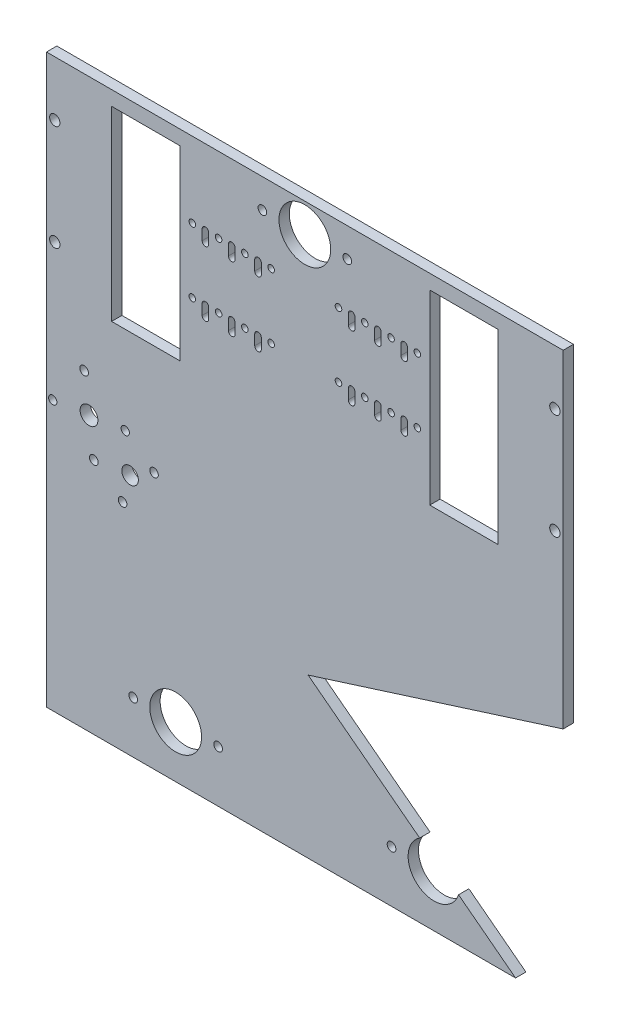
SolidWorks part; units mm, degrees
ref_plane "Front Plane" through (0, 0, 0) normal (0, 0, 1) x (1, 0, 0)
ref_plane "Top Plane" through (0, 0, 0) normal (0, 1, 0) x (1, 0, 0)
ref_plane "Right Plane" through (0, 0, 0) normal (1, 0, 0) x (0, 0, -1)
sketch "Sketch1" plane through (0, 0, 0) normal (0, 0, 1) x (1, 0, 0)
  line L0 (124.8, 0) -> (124.8, -340.9) construction
  line L1 (0, 0) -> (249.6, 0)
  line L2 (0, 0) -> (0, -340.9)
  line L3 (0, -340.9) -> (249.6, -340.9)
  line L4 (249.6, 0) -> (249.6, -340.9)
  line L9 (185.16, -7) -> (218.16, -7)
  line L10 (185.16, -7) -> (185.16, -97)
  line L11 (185.16, -97) -> (218.16, -97)
  line L12 (218.16, -7) -> (218.16, -97)
  line L13 (179.16, -52) -> (228.95, -52) construction
  line L14 (141.06, -36.375) -> (147.41, -36.375) construction
  line L15 (145.3, -14) -> (104.3, -14) construction
  line L21 (179.16, -52) -> (218.16, -52) construction
  line L25 (141.06, -67.625) -> (147.41, -67.625) construction
  line L32 (147.41, -36.375) -> (147.41, -41.375) construction
  line L33 (145.8225, -36.375) -> (145.8225, -41.375)
  line L34 (148.9975, -36.375) -> (148.9975, -41.375)
  line L35 (160.11, -36.375) -> (160.11, -41.375) construction
  line L36 (158.52, -36.375) -> (158.52, -41.375)
  line L37 (161.7, -36.375) -> (161.7, -41.375)
  line L38 (172.81, -36.375) -> (172.81, -41.375) construction
  line L39 (171.22, -36.375) -> (171.22, -41.375)
  line L40 (174.4, -36.375) -> (174.4, -41.375)
  line L41 (147.41, -36.375) -> (153.76, -36.375) construction
  line L42 (153.76, -36.375) -> (160.11, -36.375) construction
  line L43 (160.11, -36.375) -> (166.46, -36.375) construction
  line L44 (166.46, -36.375) -> (172.81, -36.375) construction
  line L45 (172.81, -36.375) -> (179.16, -36.375) construction
  line L48 (228.95, -52) -> (147.41, -52) construction
  line L52 (204.16, -7) -> (204.16, -97) construction
  line L53 (194.16, -7) -> (214.16, -7) construction
  line L54 (194.16, -7) -> (194.16, -97) construction
  line L55 (194.16, -97) -> (214.16, -97) construction
  line L56 (214.16, -7) -> (214.16, -97) construction
  line L62 (147.41, -67.625) -> (147.41, -72.625) construction
  line L65 (145.8225, -67.625) -> (145.8225, -72.625)
  line L68 (148.9975, -67.625) -> (148.9975, -72.625)
  line L71 (160.11, -67.625) -> (160.11, -72.625) construction
  line L78 (158.52, -67.625) -> (158.52, -72.625)
  line L79 (161.7, -67.625) -> (161.7, -72.625)
  line L80 (172.81, -67.625) -> (172.81, -72.625) construction
  line L83 (171.22, -67.625) -> (171.22, -72.625)
  line L87 (147.41, -52) -> (102.19, -52) construction
  line L90 (179.16, -36.375) -> (179.16, -67.625) construction
  line L93 (147.41, -36.375) -> (147.41, -52) construction
  line L102 (245.6, -26.5) -> (245.6, -77.5) construction
  line L103 (218.16, -52) -> (245.6, -52) construction
  line L105 (174.4, -67.625) -> (174.4, -72.625)
  line L106 (147.41, -67.625) -> (153.76, -67.625) construction
  line L107 (153.76, -67.625) -> (160.11, -67.625) construction
  line L108 (160.11, -67.625) -> (166.46, -67.625) construction
  line L109 (166.46, -67.625) -> (172.81, -67.625) construction
  line L110 (172.81, -67.625) -> (179.16, -67.625) construction
  line L111 (102.19, -36.375) -> (102.19, -41.375) construction
  line L112 (103.7775, -36.375) -> (103.7775, -41.375)
  line L113 (100.6025, -36.375) -> (100.6025, -41.375)
  line L114 (89.49, -36.375) -> (89.49, -41.375) construction
  line L115 (91.08, -36.375) -> (91.08, -41.375)
  line L116 (87.9, -36.375) -> (87.9, -41.375)
  line L117 (76.79, -36.375) -> (76.79, -41.375) construction
  line L118 (78.38, -36.375) -> (78.38, -41.375)
  line L119 (75.2, -36.375) -> (75.2, -41.375)
  line L120 (102.19, -67.625) -> (102.19, -72.625) construction
  line L121 (103.7775, -67.625) -> (103.7775, -72.625)
  line L122 (100.6025, -67.625) -> (100.6025, -72.625)
  line L123 (89.49, -67.625) -> (89.49, -72.625) construction
  line L124 (91.08, -67.625) -> (91.08, -72.625)
  line L125 (87.9, -67.625) -> (87.9, -72.625)
  line L126 (76.79, -67.625) -> (76.79, -72.625) construction
  line L127 (78.38, -67.625) -> (78.38, -72.625)
  line L128 (75.2, -67.625) -> (75.2, -72.625)
  line L129 (76.79, -67.625) -> (70.44, -67.625) construction
  line L130 (83.14, -67.625) -> (76.79, -67.625) construction
  line L131 (89.49, -67.625) -> (83.14, -67.625) construction
  line L132 (95.84, -67.625) -> (89.49, -67.625) construction
  line L133 (102.19, -67.625) -> (95.84, -67.625) construction
  line L134 (31.44, -52) -> (4, -52) construction
  line L135 (4, -26.5) -> (4, -77.5) construction
  line L136 (102.19, -36.375) -> (102.19, -52) construction
  line L137 (70.44, -36.375) -> (70.44, -67.625) construction
  line L139 (35.44, -7) -> (35.44, -97) construction
  line L140 (55.44, -97) -> (35.44, -97) construction
  line L141 (55.44, -7) -> (55.44, -97) construction
  line L142 (55.44, -7) -> (35.44, -7) construction
  line L143 (45.44, -7) -> (45.44, -97) construction
  line L144 (20.65, -52) -> (102.19, -52) construction
  line L145 (76.79, -36.375) -> (70.44, -36.375) construction
  line L146 (83.14, -36.375) -> (76.79, -36.375) construction
  line L147 (89.49, -36.375) -> (83.14, -36.375) construction
  line L148 (95.84, -36.375) -> (89.49, -36.375) construction
  line L149 (102.19, -36.375) -> (95.84, -36.375) construction
  line L150 (108.54, -67.625) -> (102.19, -67.625) construction
  line L151 (70.44, -52) -> (31.44, -52) construction
  line L152 (108.54, -36.375) -> (102.19, -36.375) construction
  line L153 (70.44, -52) -> (20.65, -52) construction
  line L154 (31.44, -7) -> (31.44, -97)
  line L155 (64.44, -97) -> (31.44, -97)
  line L156 (64.44, -7) -> (64.44, -97)
  line L157 (64.44, -7) -> (31.44, -7)
  arc A6 (174.4, -36.375) -> (171.22, -36.375) centre (172.81, -36.375) cw construction
  arc A7 (171.22, -36.375) -> (174.4, -36.375) centre (172.81, -36.375) cw
  arc A10 (158.52, -36.375) -> (161.7, -36.375) centre (160.11, -36.375) cw
  arc A11 (161.7, -36.375) -> (158.52, -36.375) centre (160.11, -36.375) cw construction
  arc A14 (145.8225, -36.375) -> (148.9975, -36.375) centre (147.41, -36.375) cw
  arc A15 (148.9975, -36.375) -> (145.8225, -36.375) centre (147.41, -36.375) cw construction
  circle A38 centre (104.3, -14) radius 2.1
  arc A39 (148.9975, -41.375) -> (145.8225, -41.375) centre (147.41, -41.375) cw
  arc A41 (161.7, -41.375) -> (158.52, -41.375) centre (160.11, -41.375) cw
  arc A43 (174.4, -41.375) -> (171.22, -41.375) centre (172.81, -41.375) cw
  circle A84 centre (245.6, -26.5) radius 2.5
  circle A85 centre (245.6, -77.5) radius 2.5
  circle A109 centre (145.3, -14) radius 2.1
  circle A179 centre (179.16, -36.375) radius 1.59
  arc A182 (174.4, -67.625) -> (171.22, -67.625) centre (172.81, -67.625) cw construction
  arc A183 (171.22, -67.625) -> (174.4, -67.625) centre (172.81, -67.625) cw
  arc A184 (158.52, -67.625) -> (161.7, -67.625) centre (160.11, -67.625) cw
  arc A185 (161.7, -67.625) -> (158.52, -67.625) centre (160.11, -67.625) cw construction
  arc A188 (145.8225, -67.625) -> (148.9975, -67.625) centre (147.41, -67.625) cw
  arc A189 (148.9975, -67.625) -> (145.8225, -67.625) centre (147.41, -67.625) cw construction
  arc A193 (148.9975, -72.625) -> (145.8225, -72.625) centre (147.41, -72.625) cw
  arc A195 (161.7, -72.625) -> (158.52, -72.625) centre (160.11, -72.625) cw
  arc A197 (174.4, -72.625) -> (171.22, -72.625) centre (172.81, -72.625) cw
  circle A198 centre (179.16, -67.625) radius 1.59
  circle A199 centre (124.8, -14) radius 12.5
  circle A200 centre (141.06, -36.375) radius 1.59
  circle A201 centre (153.76, -36.375) radius 1.59
  circle A202 centre (166.46, -36.375) radius 1.59
  circle A203 centre (141.06, -67.625) radius 1.59
  circle A204 centre (153.76, -67.625) radius 1.59
  circle A205 centre (166.46, -67.625) radius 1.59
  arc A206 (103.7775, -36.375) -> (100.6025, -36.375) centre (102.19, -36.375) ccw
  arc A207 (100.6025, -41.375) -> (103.7775, -41.375) centre (102.19, -41.375) ccw
  arc A208 (91.08, -36.375) -> (87.9, -36.375) centre (89.49, -36.375) ccw
  arc A209 (87.9, -41.375) -> (91.08, -41.375) centre (89.49, -41.375) ccw
  arc A210 (78.38, -36.375) -> (75.2, -36.375) centre (76.79, -36.375) ccw
  arc A211 (75.2, -41.375) -> (78.38, -41.375) centre (76.79, -41.375) ccw
  arc A212 (103.7775, -67.625) -> (100.6025, -67.625) centre (102.19, -67.625) ccw
  arc A213 (100.6025, -72.625) -> (103.7775, -72.625) centre (102.19, -72.625) ccw
  arc A214 (91.08, -67.625) -> (87.9, -67.625) centre (89.49, -67.625) ccw
  arc A215 (87.9, -72.625) -> (91.08, -72.625) centre (89.49, -72.625) ccw
  arc A216 (78.38, -67.625) -> (75.2, -67.625) centre (76.79, -67.625) ccw
  arc A217 (75.2, -72.625) -> (78.38, -72.625) centre (76.79, -72.625) ccw
  arc A218 (100.6025, -67.625) -> (103.7775, -67.625) centre (102.19, -67.625) ccw construction
  arc A219 (87.9, -67.625) -> (91.08, -67.625) centre (89.49, -67.625) ccw construction
  arc A220 (75.2, -67.625) -> (78.38, -67.625) centre (76.79, -67.625) ccw construction
  arc A221 (100.6025, -36.375) -> (103.7775, -36.375) centre (102.19, -36.375) ccw construction
  arc A222 (87.9, -36.375) -> (91.08, -36.375) centre (89.49, -36.375) ccw construction
  arc A223 (75.2, -36.375) -> (78.38, -36.375) centre (76.79, -36.375) ccw construction
  circle A224 centre (83.14, -67.625) radius 1.59
  circle A225 centre (95.84, -67.625) radius 1.59
  circle A226 centre (108.54, -67.625) radius 1.59
  circle A227 centre (83.14, -36.375) radius 1.59
  circle A228 centre (95.84, -36.375) radius 1.59
  circle A229 centre (108.54, -36.375) radius 1.59
  circle A230 centre (70.44, -67.625) radius 1.59
  circle A234 centre (70.44, -36.375) radius 1.59
  circle A236 centre (4, -77.5) radius 2.5
  circle A237 centre (4, -26.5) radius 2.5
  point P64 (147.41, -52)
  point P65 (102.19, -38.875)
  point P69 (228.95, -52)
  point P71 (221, -87.34)
  point P76 (233.7, -87.34)
  point P78 (221, -54.5)
  point P82 (233.7, -54.5)
  point P86 (246.4, -54.5)
  point P93 (179.16, -52)
  point P97 (246.4, -87.34)
  point P104 (89.49, -38.875)
  point P111 (76.79, -38.875)
  point P119 (102.19, -70.125)
  point P126 (89.49, -70.125)
  point P133 (76.79, -70.125)
  point P155 (124.8, -76.5574)
  point P166 (124.8, -52)
  point P183 (124.8, -76.5574)
  point P199 (70.44, -52)
  point P200 (20.65, -52)
  point P201 (102.19, -52)
  dimension "D5" = 20
  dimension "D10" = 5
  dimension "D12" = 3.18
  dimension "D15" = 5
  dimension "D16" = 5
  dimension "D19" = 3.18
  dimension "D20" = 1.5875
  dimension "D21" = 3.18
  dimension "D22" = 1.59
  dimension "D23" = 3.18
  dimension "D24" = 1.59
  dimension "D25" = 3.18
  dimension "D33" = 3.18
  dimension "D34" = 5
  dimension "D35" = 4.2
  dimension "D32" = 1.5875
  dimension "D36" = 1.59
  dimension "D37" = 3.18
  dimension "D39" = 1.59
  dimension "D47" = 3.18
  dimension "D49" = 25
  dimension "D51" = 4.2
  dimension "D1" = 249.6
  dimension "D2" = 340.9
  dimension "D3" = 4
  dimension "D4" = 90
  dimension "D6" = 90
  dimension "D7" = 9
  dimension "D8" = 6
  dimension "D9" = 5
  dimension "D11" = 6.35
  dimension "D13" = 6.35
  dimension "D14" = 89.36
  dimension "D17" = 25.5
  dimension "D18" = 4
  dimension "D26" = 5
  dimension "D27" = 6.35
  dimension "D28" = 6.35
  dimension "D29" = 6.35
  dimension "D30" = 6.35
  dimension "D31" = 6.35
  dimension "D38" = 7
  dimension "D40" = 5
  dimension "D41" = 6.35
  dimension "D42" = 6.35
  dimension "D43" = 6.35
  dimension "D44" = 6.35
  dimension "D45" = 6.35
  dimension "D46" = 5
  dimension "D48" = 31.25
  dimension "D50" = 20.5
  dimension "14" = 14
extrude "Boss-Extrude1" add sketch "Sketch1" along normal blind 5
sketch "Sketch2" plane through (0, 0, 5) normal (0, 0, 1) x (1, 0, 0)
  line L0 (-27.1214, -80.1211) -> (54.8789, 27.1214) construction
  line L1 (277.1296, -312.7589) -> (359.1299, -205.5164) construction
  line L2 (-27.1214, -80.1211) -> (277.1296, -312.7589) construction
  line L3 (92.2198, 60.8405) -> (87.5714, 58.9986) construction
  line L4 (87.5714, 58.9986) -> (112.9306, -5) construction
  line L5 (120.7692, -11.2093) -> (92.2198, 60.8405) construction
  line L6 (54.8789, 27.1214) -> (359.1299, -205.5164) construction
  line L7 (51.8418, 23.1494) -> (356.0928, -209.4884) construction
  line L8 (-24.0843, -76.1492) -> (280.1666, -308.787) construction
  line L9 (92.2198, 60.8405) -> (96.8682, 62.6824) construction
  line L10 (96.8682, 62.6824) -> (122.2273, -1.3162) construction
  line L11 (178.4848, -231.0386) -> (254.411, -131.74) construction
  line L12 (117.1493, -105.4631) -> (216.4479, -181.3893) construction
  line L13 (79.1862, -155.1124) -> (155.1124, -55.8138) construction
  line L14 (249.6, 0) -> (0, 0) construction
  line L15 (0, 0) -> (0, -340.9) construction
  line L16 (5, -130) -> (130, -130) construction
  line L17 (5, -340.9) -> (5, 0) construction
  line L18 (130, -340.9) -> (130, 0) construction
  line L19 (0, -340.9) -> (0, 0) construction
  line L20 (135, -340.9) -> (135, 0) construction
  line L21 (0, -340.9) -> (33.4202, -340.9) construction
  line L22 (33.4202, -340.9) -> (130, -340.9) construction
  line L23 (130, -340.9) -> (135, -340.9) construction
  line L24 (0, -340.9) -> (249.6, -340.9) construction
  line L25 (0, 0) -> (5, 0) construction
  line L26 (5, 0) -> (130, 0) construction
  line L27 (130, 0) -> (135, 0) construction
  line L28 (249.6, -98.5967) -> (312.6149, -98.5967) construction
  line L29 (249.6, -340.9) -> (249.6, 0) construction
  line L30 (249.6, -158.6746) -> (295.6765, -158.6746) construction
  line L31 (185.16, -97) -> (218.16, -97) construction
  line L32 (194.16, -7.496) -> (194.16, -96.496) construction
  line L33 (180.868, -232.8608) -> (256.7942, -133.5622) construction
  line L34 (249.6, -283.6746) -> (0, -283.6746) construction
  line L35 (0, -5) -> (249.6, -5) construction
  line L36 (249.6, 0) -> (249.6, -5) construction
  line L37 (249.6, -5) -> (249.6, -340.9) construction
  line L38 (249.6, -340.9) -> (5, -340.9) construction
  line L39 (5, -340.9) -> (0, -340.9) construction
  line L40 (0, -335.9) -> (249.6, -335.9) construction
  line L41 (244.6, -340.9) -> (244.6, 0) construction
  circle A0 centre (67.5, -67.5) radius 62.5 construction
  circle A1 centre (268.4804, -221.1746) radius 62.5 construction
  circle A2 centre (67.5, -67.5) radius 67.5 construction
  circle A3 centre (166.7986, -143.4262) radius 62.5 construction
  circle A4 centre (120.7692, -11.2093) radius 77.5 construction
  circle A5 centre (120.7692, -11.2093) radius 2.5 construction
  circle A6 centre (111.5597, 12.0326) radius 1.5 construction
  arc A7 (112.9306, -5) -> (122.2273, -1.3162) centre (120.7692, -11.2093) ccw construction
  point P49 (194.16, -97)
  dimension "D1" = 125
  dimension "D2" = 125
  dimension "D3" = 5
  dimension "D6" = 3
  dimension "D7" = 10
  dimension "D10" = 125
  dimension "D8" = 5
  dimension "D11" = 3
  dimension "D4" = 5
  dimension "D5" = 25
  dimension "D9" = 5
  dimension "D12" = 14
  dimension "D13" = 5
  dimension "D14" = 5
  dimension "D15" = 5
  dimension "D16" = 5
  dimension "D17" = 5
sketch "Sketch4" plane through (0, 0, 5) normal (0, 0, 1) x (1, 0, 0)
  line L3 (249.6, -161.5945) -> (249.6, -280.7546)
  line L5 (249.6, -340.9) -> (249.6, 0) construction
  arc A0 (249.6, -161.5945) -> (249.6, -280.7546) centre (268.4804, -221.1746) ccw
  circle A1 centre (268.4804, -221.1746) radius 62.5 construction
extrude "Cut-Extrude3" cut sketch "Sketch4" along normal blind 193 and the other way blind 193
sketch "Sketch7" plane through (0, 0, 5) normal (0, 0, 1) x (1, 0, 0)
  line L0 (249.6, -158.4475) -> (126.3826, -197.4941)
  line L1 (249.6, -340.9) -> (249.6, -280.7546) construction
  line L2 (126.3826, -197.4941) -> (249.6, -158.4475) construction
  line L3 (-27.1214, -80.1211) -> (277.1296, -312.7589) construction
  line L4 (126.3826, -197.4941) -> (226.6086, -274.1293)
  line L5 (249.6, -158.4475) -> (249.6, -340.9)
  line L6 (249.6, -340.9) -> (0, -340.9)
  line L7 (0, -340.9) -> (0, -274.1293)
  line L10 (0, -340.9) -> (249.6, -340.9) construction
  line L11 (0, 0) -> (0, -340.9) construction
  line L12 (226.6086, -274.1293) -> (0, -274.1293)
extrude "Cut-Extrude6" cut sketch "Sketch7" against normal through all
sketch "Sketch8" plane through (0, 0, 5) normal (0, 0, 1) x (1, 0, 0)
  circle A0 centre (3.009, -144.0715) radius 2
  circle A1 centre (18.1942, -124.2118) radius 2.1
  circle A2 centre (22.8687, -159.2567) radius 2.1
  circle A3 centre (36.7705, -169.8864) radius 2.0586
  circle A4 centre (40.3912, -156.9195) radius 4
  circle A5 centre (38.054, -139.397) radius 2
  circle A6 centre (20.5315, -141.7343) radius 4.3
  circle A7 centre (51.9558, -150.0267) radius 2.0586
  circle A8 centre (36.7705, -169.8864) radius 2.0586 construction
  circle A9 centre (51.9558, -150.0267) radius 2.0586 construction
  circle A10 centre (22.8687, -159.2567) radius 2.1 construction
  circle A11 centre (3.009, -144.0715) radius 2 construction
  circle A12 centre (18.1942, -124.2118) radius 2.1 construction
  circle A13 centre (40.3912, -156.9195) radius 4 construction
  circle A15 centre (20.5315, -141.7343) radius 4.3 construction
  circle A16 centre (38.054, -139.397) radius 2 construction
extrude "Cut-Extrude7" cut sketch "Sketch8" against normal through all
sketch "Sketch9" plane through (0, 0, 5) normal (0, 0, 1) x (1, 0, 0)
  line L0 (124.8, 0) -> (124.8, -274.1293) construction
  line L1 (249.6, 0) -> (0, 0) construction
  line L2 (226.6086, -274.1293) -> (0, -274.1293) construction
  line L3 (0, -340.9) -> (0, 0) construction
  line L4 (249.6, -158.4475) -> (249.6, 0) construction
  line L5 (62.4, 0) -> (62.4, -274.1293) construction
  line L6 (5, 0) -> (130, 0) construction
  line L7 (41.9, -249.1293) -> (62.4, -249.1293) construction
  line L8 (62.4, -249.1293) -> (82.8847, -249.1293) construction
  line L9 (187.2, -249.1293) -> (166.7153, -249.1293) construction
  line L10 (207.7, -249.1293) -> (187.2, -249.1293) construction
  line L11 (187.2, 0) -> (187.2, -274.1293) construction
  line L12 (203.213, -226.1461) -> (217.7896, -262.8837) construction
  circle A0 centre (62.4, -249.1293) radius 12.5
  circle A2 centre (82.9, -249.1293) radius 2.1
  circle A3 centre (41.9, -249.1293) radius 2.1
  circle A4 centre (207.7, -249.1293) radius 2.1
  circle A5 centre (166.7, -249.1293) radius 2.1
  circle A6 centre (187.2, -249.1293) radius 12.5
  circle A8 centre (268.4804, -221.1746) radius 62.5 construction
  dimension "D1" = 25
  dimension "D2" = 4.2
  dimension "D3" = 4.2
  dimension "D7" = 25
  dimension "D4" = 62.4
  dimension "D5" = 20.5
  dimension "D6" = 20.5
extrude "Cut-Extrude8" cut sketch "Sketch9" against normal through all
